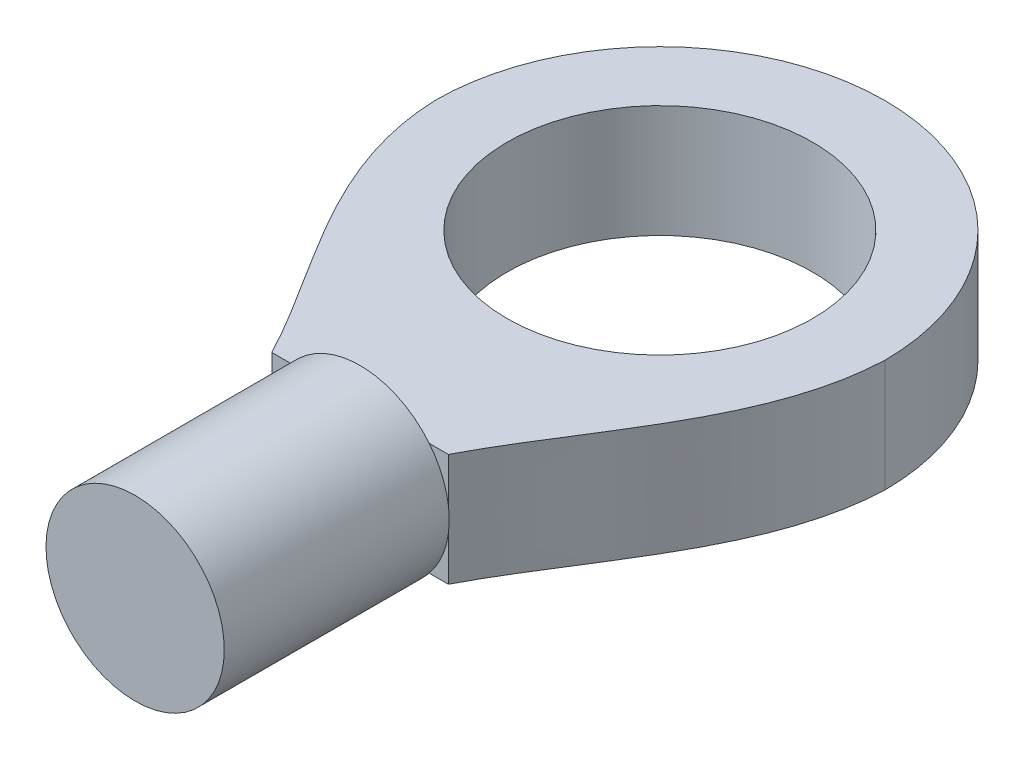
SolidWorks part; units mm, degrees
ref_plane "Front Plane" through (0, 0, 0) normal (0, 0, 1) x (1, 0, 0)
ref_plane "Top Plane" through (0, 0, 0) normal (0, 1, 0) x (1, 0, 0)
ref_plane "Right Plane" through (0, 0, 0) normal (1, 0, 0) x (0, 0, -1)
sketch "Sketch2" plane through (0, 0, 0) normal (0, 1, 0) x (1, 0, 0)
  line L0 (-4.71, -15.99) -> (4.71, -15.99)
  line L1 (0, 0) -> (0, -15.99) construction
  line L2 (0, -15.99) -> (0, -40.99)
  circle A0 centre (0, 0) radius 8.15
  arc A1 (12, 0) -> (-12, 0) centre (0, 0) ccw
  spline S0 degree 3 poles (-12, 0) (-11.768, -6.147) (-7.3273, -10.9528) (-4.71, -15.99) knots 0 0 0 0 0.424868 0.424868 0.424868 0.424868
  spline S1 degree 3 poles (12, 0) (11.768, -6.147) (7.3273, -10.9528) (4.71, -15.99) knots 0 0 0 0 0.424868 0.424868 0.424868 0.424868
  point P5 (0, -15.99)
  dimension "D1" = 16.3
  dimension "D5" = 25
  dimension "D4" = 24
  dimension "D2" = 9.42
  dimension "D3" = 15.99
extrude "Boss-Extrude1" add sketch "Sketch2" along normal blind 6
ref_plane "Plane1" through (0, 0, 15.99) normal (0, 0, 1) x (1, 0, 0)
sketch "Sketch3" plane through (0, 0, 15.99) normal (0, 0, 1) x (1, 0, 0)
  line L0 (-4.71, 6) -> (4.71, 0) construction
  circle A0 centre (0, 3) radius 4.755
  dimension "D1" = 9.51
extrude "Boss-Extrude2" add sketch "Sketch3" along normal blind 12
